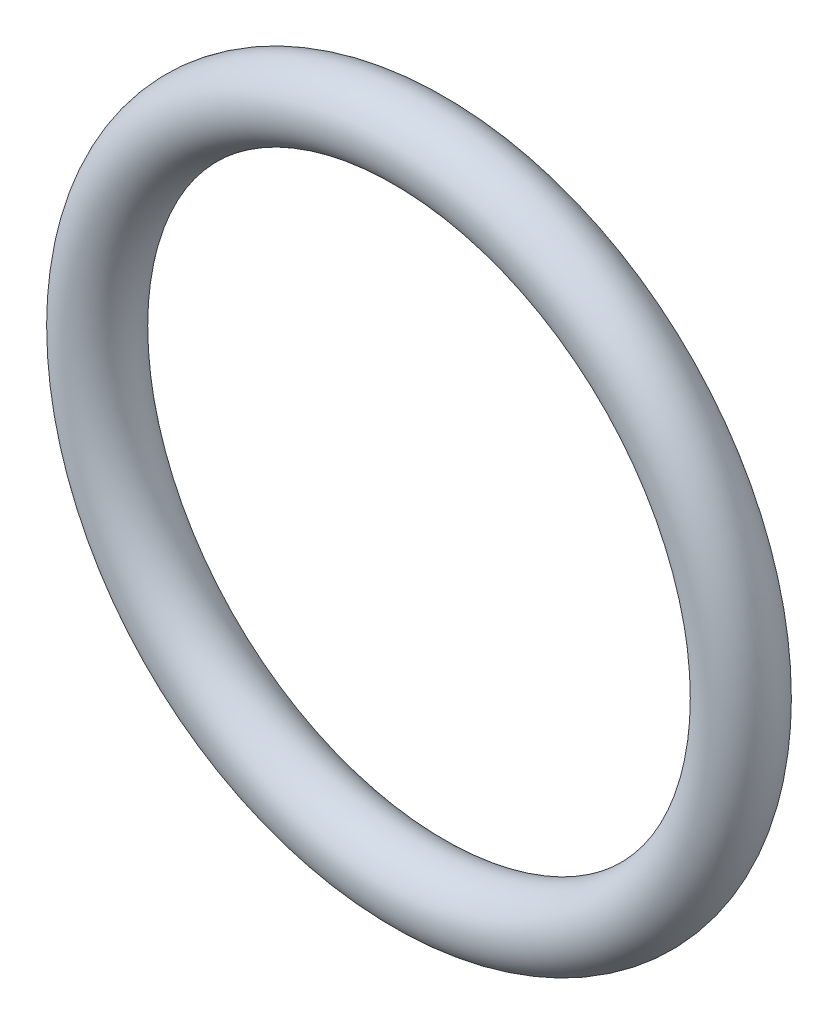
SolidWorks part; units mm, degrees
ref_plane "Front Plane" through (0, 0, 0) normal (0, 0, 1) x (1, 0, 0)
ref_plane "Top Plane" through (0, 0, 0) normal (0, 1, 0) x (1, 0, 0)
ref_plane "Right Plane" through (0, 0, 0) normal (1, 0, 0) x (0, 0, -1)
sketch "Sketch1" plane through (0, 0, 0) normal (0, 1, 0) x (1, 0, 0)
  line L0 (0, -36.15) -> (0, -37.65) construction
  circle A0 centre (6.75, -36.9) radius 0.75
revolve "Revolve1" add sketch "Sketch1" angle 360 about L0
